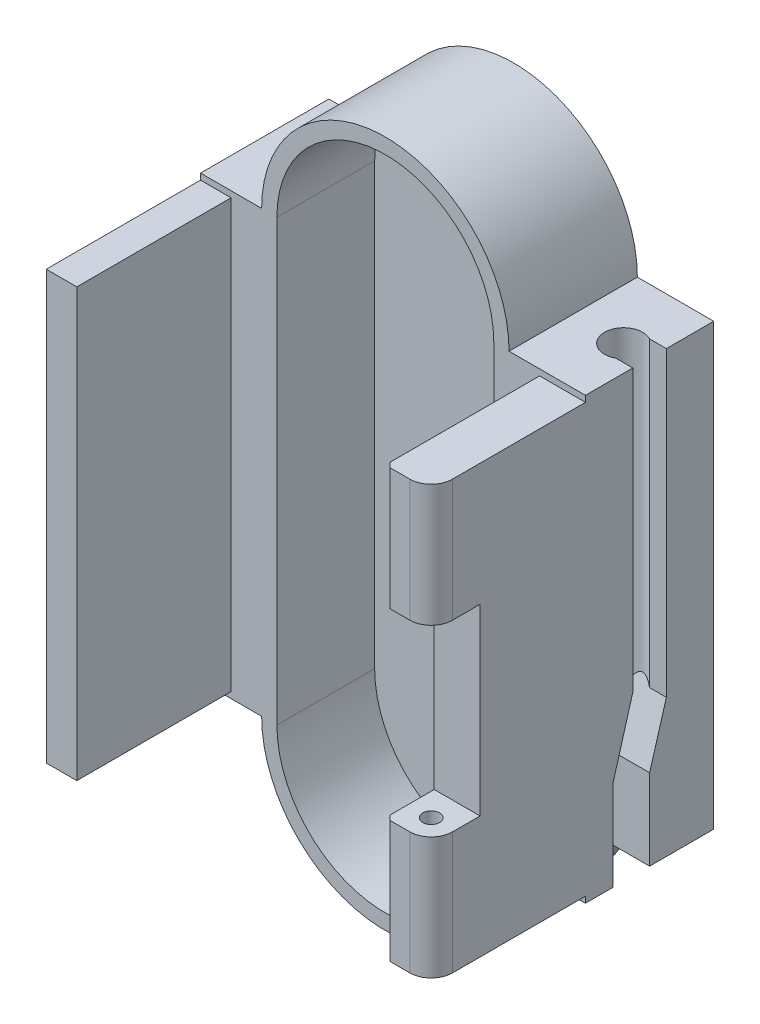
SolidWorks part; units mm, degrees
ref_plane "Front" through (0, 0, 0) normal (0, 0, 1) x (1, 0, 0)
ref_plane "Top" through (0, 0, 0) normal (0, 1, 0) x (1, 0, 0)
ref_plane "Right" through (0, 0, 0) normal (1, 0, 0) x (0, 0, -1)
sketch "草图1" plane through (0, 0, 0) normal (0, 0, 1) x (1, 0, 0)
  line L1 (0, 0) -> (24.2, 0)
  line L2 (0, 0) -> (0, -45)
  line L3 (0, -45) -> (24.2, -45)
  line L4 (24.2, 0) -> (24.2, -45)
  dimension "D1" = 24.2
  dimension "D2" = 45
extrude "凸台-拉伸1" add sketch "草图1" along normal blind 18.5
sketch "草图2" plane through (0, 0, 18.5) normal (0, 0, 1) x (1, 0, 0)
  line L0 (0, 0) -> (0, -8.5)
  line L1 (0, 0) -> (0, -45) construction
  line L2 (0, -8.5) -> (2, -8.5)
  line L3 (2, -8.5) -> (2, -36.5)
  line L4 (2, -36.5) -> (0, -36.5)
  line L5 (0, -36.5) -> (0, -45)
  line L6 (0, -45) -> (24.2, -45)
  line L7 (24.2, -45) -> (24.2, -36.5)
  line L8 (24.2, -45) -> (24.2, 0) construction
  line L9 (24.2, -36.5) -> (22.2, -36.5)
  line L10 (22.2, -36.5) -> (22.2, -8.5)
  line L11 (22.2, -8.5) -> (24.2, -8.5)
  line L12 (24.2, -8.5) -> (24.2, 0)
  line L13 (24.2, 0) -> (0, 0)
  dimension "D1" = 2
  dimension "D2" = 2
  dimension "D3" = 28
  dimension "D4" = 28
  dimension "D5" = 8.5
  dimension "D6" = 8.5
extrude "切除-拉伸1" cut sketch "草图2" against normal blind 10.1
sketch "草图3" plane through (0, 0, 8.4) normal (0, 0, 1) x (1, 0, 0)
  line L2 (5, -8.1) -> (5, -36.9)
  line L4 (19.2, -8.1) -> (19.2, -36.9)
  line L5 (24.2, -8.5) -> (24.2, 0) construction
  arc A0 (19.2, -8.1) -> (5, -8.1) centre (12.1, -8.1) ccw
  arc A1 (5, -36.9) -> (19.2, -36.9) centre (12.1, -36.9) ccw
  point P8 (24.2, -4.25)
  dimension "D5" = 14.2
  dimension "D6" = 14.2
  dimension "D7" = 7.1
  dimension "D8" = 7.1
  dimension "D4" = 5
extrude "切除-拉伸2" cut sketch "草图3" against normal blind 6.4
sketch "草图4" plane through (0, 0, 8.4) normal (0, 0, 1) x (1, 0, 0)
  line L0 (4, -8.1) -> (0, -8.1)
  line L1 (0, 0) -> (0, -8.5) construction
  line L2 (0, -8.1) -> (0, 0)
  line L3 (0, 0) -> (12.1, 0)
  line L4 (4, -36.9) -> (0, -36.9)
  line L6 (0, -36.5) -> (0, -45) construction
  line L7 (0, -36.9) -> (0, -45)
  line L8 (0, -45) -> (12.1, -45)
  arc A0 (12.1, 0) -> (4, -8.1) centre (12.1, -8.1) ccw
  arc A1 (4, -36.9) -> (12.1, -45) centre (12.1, -36.9) ccw
extrude "切除-拉伸3" cut sketch "草图4" against normal through all
sketch "草图5" plane through (0, 0, 8.4) normal (0, 0, 1) x (1, 0, 0)
  line L0 (20.2, -36.9) -> (24.2, -36.9)
  line L1 (24.2, -45) -> (24.2, -36.5) construction
  line L2 (24.2, -36.9) -> (24.2, -45)
  line L3 (24.2, -45) -> (12.1, -45)
  line L4 (20.2, -8.1) -> (24.2, -8.1)
  line L5 (24.2, -8.5) -> (24.2, 0) construction
  line L6 (24.2, -8.1) -> (24.2, 0)
  line L7 (24.2, 0) -> (12.1, 0)
  arc A0 (20.2, -8.1) -> (12.1, 0) centre (12.1, -8.1) ccw
  arc A1 (12.1, -45) -> (20.2, -36.9) centre (12.1, -36.9) ccw
extrude "切除-拉伸4" cut sketch "草图5" against normal through all
sketch "草图6" plane through (24.2, 0, 0) normal (1, 0, 0) x (0, 0, -1)
  line L0 (0, -36.9) -> (0, -8.1) construction
  line L1 (-6.6, -34.5) -> (-4.2, -34.5)
  line L2 (-6.6, -34.5) -> (-6.6, -36.9)
  line L3 (-6.6, -36.9) -> (-4.2, -36.9)
  line L4 (-4.2, -34.5) -> (-4.2, -36.9)
  line L6 (0, -36.9) -> (-8.4, -36.9) construction
  dimension "D1" = 2.4
  dimension "D2" = 4.2
  dimension "D3" = 0
  dimension "D4" = 2.4
extrude "切除-拉伸5" cut sketch "草图6" against normal blind 6.4
sketch "草图8" plane through (0, 0, 8.4) normal (0, 0, 1) x (1, 0, 0)
  line L1 (19.2, -36.9) -> (22.6, -36.9)
  line L2 (19.2, -36.9) -> (19.2, -34.5)
  line L3 (19.2, -34.5) -> (22.6, -34.5)
  line L4 (22.6, -36.9) -> (22.6, -34.5)
  dimension "D1" = 2.4
  dimension "D2" = 3.4
extrude "切除-拉伸7" cut sketch "草图8" against normal blind 2
sketch "草图9" plane through (22.2, 0, 0) normal (-1, 0, 0) x (0, 0, 1)
  line L1 (8.4, -36.5) -> (10.9, -36.5)
  line L2 (8.4, -36.5) -> (8.4, -34.5)
  line L3 (8.4, -34.5) -> (10.9, -34.5)
  line L4 (10.9, -36.5) -> (10.9, -34.5)
  dimension "D1" = 2.5
  dimension "D2" = 2
extrude "切除-拉伸8" cut sketch "草图9" against normal blind 0.4
sketch "草图12" plane through (24.2, 0, 0) normal (1, 0, 0) x (0, 0, -1)
  line L0 (-4.2, -34.5) -> (-6.6, -34.5) construction
  line L1 (0, -8.1) -> (-18.5, -8.1)
  line L2 (0, -8.1) -> (0, -34.5)
  line L3 (0, -34.5) -> (-18.5, -34.5)
  line L4 (-18.5, -8.1) -> (-18.5, -34.5)
  dimension "D1" = 18.5
  dimension "D2" = 0
extrude "凸台-拉伸2" add sketch "草图12" along normal blind 1
sketch "草图13" plane through (0, -8.1, 0) normal (0, 1, 0) x (1, 0, 0)
  line L0 (25.2, 0) -> (25.2, -18.5) construction
  line L1 (20.2, 0) -> (25.2, 0) construction
  circle A0 centre (23.5, -4.2) radius 1.25
  dimension "D1" = 2.5
  dimension "D2" = 1.7
  dimension "D3" = 4.2
extrude "切除-拉伸10" cut sketch "草图13" against normal up to surface (26.4 mm away) up to face at (22.9333, -34.5, 8.1)
sketch "草图14" plane through (25.2, 0, 0) normal (1, 0, 0) x (0, 0, -1)
  line L0 (0, -8.1) -> (-18.5, -8.1) construction
  line L1 (-5.3, -8.1) -> (-3.1, -8.1)
  line L2 (-5.3, -8.1) -> (-5.3, -34.5)
  line L3 (-5.3, -34.5) -> (-3.1, -34.5)
  line L4 (-3.1, -8.1) -> (-3.1, -34.5)
  line L5 (-18.5, -34.5) -> (0, -34.5) construction
  line L6 (0, -34.5) -> (0, -8.1) construction
  dimension "D1" = 2.2
  dimension "D2" = 3.1
extrude "切除-拉伸11" cut sketch "草图14" against normal blind 1.5
sketch "草图17" plane through (25.2, 0, 0) normal (1, 0, 0) x (0, 0, -1)
  line L0 (-6.6, -34.5) -> (-6.6, -31)
  line L1 (-6.6, -31) -> (-5.3, -26.5)
  line L2 (-4.2, -26.5) -> (-4.2, -34.5)
  line L3 (-5.3, -26.5) -> (-4.2, -26.5)
  line L5 (-4.2, -34.5) -> (-6.6, -34.5)
  dimension "D1" = 1.1
  dimension "D2" = 3.5
extrude "切除-拉伸13" cut sketch "草图17" against normal blind 2.95
sketch "草图19" plane through (24.2, 0, 0) normal (1, 0, 0) x (0, 0, -1)
  line L1 (-18.5, -36.5) -> (-8.4, -36.5)
  line L2 (-18.5, -36.5) -> (-18.5, -34.5)
  line L3 (-18.5, -34.5) -> (-8.4, -34.5)
  line L4 (-8.4, -36.5) -> (-8.4, -34.5)
extrude "凸台-拉伸3" add sketch "草图19" along normal blind 1
sketch "草图20" plane through (24.2, 0, 0) normal (1, 0, 0) x (0, 0, -1)
  line L1 (-8.4, -36.9) -> (-6.6, -36.9)
  line L2 (-8.4, -36.9) -> (-8.4, -34.5)
  line L3 (-8.4, -34.5) -> (-6.6, -34.5)
  line L4 (-6.6, -36.9) -> (-6.6, -34.5)
extrude "凸台-拉伸4" add sketch "草图20" along normal blind 1
sketch "草图21" plane through (0, -8.1, 0) normal (0, 1, 0) x (1, 0, 0)
  line L1 (25.2, -18.5) -> (24.2, -18.5)
  line L2 (25.2, -18.5) -> (25.2, -8.4)
  line L3 (25.2, -8.4) -> (24.2, -8.4)
  line L4 (24.2, -18.5) -> (24.2, -8.4)
extrude "切除-拉伸14" cut sketch "草图21" against normal up to surface (0.4 mm away) up to face at (23.2, -8.5, 13.45)
sketch "草图22" plane through (24.2, 0, 0) normal (1, 0, 0) x (0, 0, -1)
  line L1 (0, -36.9) -> (-4.2, -36.9)
  line L2 (0, -36.9) -> (0, -34.5)
  line L3 (0, -34.5) -> (-4.2, -34.5)
  line L4 (-4.2, -36.9) -> (-4.2, -34.5)
extrude "凸台-拉伸5" add sketch "草图22" along normal blind 1
sketch "草图23" plane through (22.25, 0, 0) normal (1, 0, 0) x (0, 0, -1)
  line L1 (-4.2, -34.5) -> (-2.4, -34.5)
  line L2 (-4.2, -34.5) -> (-4.2, -31.6)
  line L4 (-2.4, -34.5) -> (-2.4, -25.5)
  line L5 (-4.2, -34.5) -> (-4.2, -26.5) construction
  line L6 (-4.2, -31.6) -> (-2.4, -25.5)
  dimension "D1" = 1.8
  dimension "D2" = 2.9
  dimension "D3" = 9
extrude "凸台-拉伸6" add sketch "草图23" along normal up to surface (2.95 mm away) up to face at (25.2, -26.5, 2.4333)
sketch "草图25" plane through (0, 0, 18.5) normal (0, 0, 1) x (1, 0, 0)
  line L0 (22.2, -34.5) -> (22.2, -8.5) construction
  line L1 (22.2, -16.5) -> (25.2, -16.5)
  line L2 (22.2, -16.5) -> (22.2, -28.5)
  line L3 (22.2, -28.5) -> (25.2, -28.5)
  line L4 (25.2, -16.5) -> (25.2, -28.5)
  line L5 (25.2, -8.5) -> (25.2, -36.5) construction
  line L6 (22.2, -8.5) -> (25.2, -8.5) construction
  line L7 (25.2, -36.5) -> (22.2, -36.5) construction
  dimension "D1" = 8
  dimension "D2" = 8
extrude "切除-拉伸15" cut sketch "草图25" against normal blind 3.2
sketch "草图26" plane through (0, -36.5, 0) normal (0, -1, 0) x (1, 0, 0)
  line L0 (25.2, 18.5) -> (25.2, 8.4) construction
  line L1 (25.2, 18.5) -> (22.2, 18.5) construction
  circle A0 centre (23.7, 17) radius 0.55
  dimension "D1" = 1.1
  dimension "D2" = 1.5
  dimension "D3" = 1.5
extrude "切除-拉伸16" cut sketch "草图26" against normal blind 26
fillet "圆角1" radius 1.4 2 edges at (25.2, -12.5, 18.5) (25.2, -32.5, 18.5)
sketch "草图27" plane through (0, 0, 0) normal (-1, 0, 0) x (0, 0, 1)
  line L0 (0, -8.1) -> (0, -36.9) construction
  line L1 (15, -10.5) -> (17, -10.5)
  line L2 (15, -10.5) -> (15, -17.5)
  line L3 (15, -17.5) -> (17, -17.5)
  line L4 (17, -10.5) -> (17, -17.5)
  line L5 (15, -27.5) -> (17, -27.5)
  line L6 (15, -27.5) -> (15, -34.5)
  line L7 (15, -34.5) -> (17, -34.5)
  line L8 (17, -27.5) -> (17, -34.5)
  line L10 (8.4, -8.5) -> (18.5, -8.5) construction
  line L11 (8.4, -36.5) -> (18.5, -36.5) construction
  dimension "D1" = 2
  dimension "D2" = 15
  dimension "D3" = 15
  dimension "D4" = 7
  dimension "D5" = 7
  dimension "D6" = 2
  dimension "D7" = 2
  dimension "D8" = 2
extrude "切除-拉伸17" cut sketch "草图27" against normal blind 1.2
chamfer "倒角1" distance 0.3 angle 45 2 edges at (22.2, -32.5, 18.5) (22.2, -12.5, 18.5)
